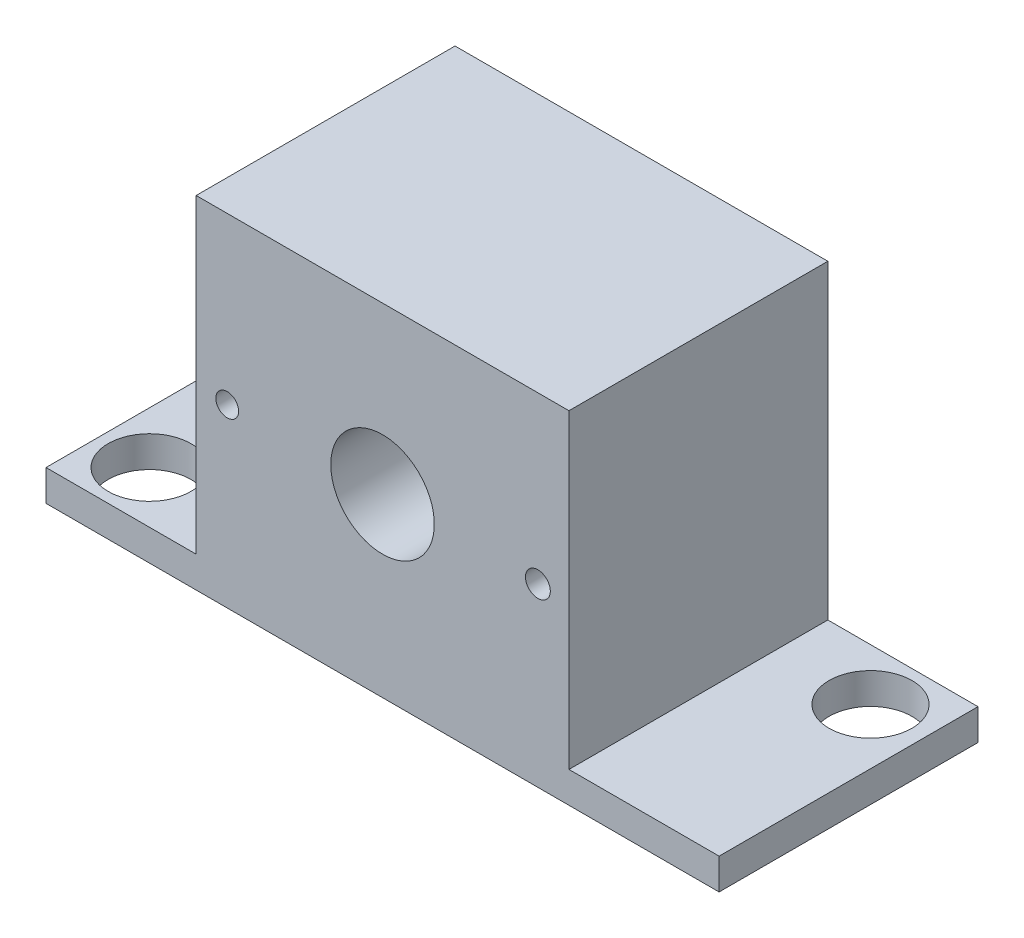
SolidWorks part; units mm, degrees
ref_plane "Front Plane" through (0, 0, 0) normal (0, 0, 1) x (1, 0, 0)
ref_plane "Top Plane" through (0, 0, 0) normal (0, 1, 0) x (1, 0, 0)
ref_plane "Right Plane" through (0, 0, 0) normal (1, 0, 0) x (0, 0, -1)
sketch "Sketch1" plane through (0, 0, 0) normal (0, 1, 0) x (1, 0, 0)
  line L1 (-32.5, 12.5) -> (32.5, 12.5)
  line L2 (-32.5, 12.5) -> (-32.5, -12.5)
  line L3 (-32.5, -12.5) -> (32.5, -12.5)
  line L4 (32.5, 12.5) -> (32.5, -12.5)
  line L5 (-32.5, 12.5) -> (32.5, -12.5) construction
  line L6 (-32.5, -12.5) -> (32.5, 12.5) construction
  circle A0 centre (-27.5, -7.5) radius 4
  circle A1 centre (27.1197, 7.5) radius 4
  point P0 (0, 0)
  dimension "D5" = 8
  dimension "D6" = 8
  dimension "D1" = 25
  dimension "D2" = 65
  dimension "D3" = 56.642
  dimension "D4" = 5
  dimension "D7" = 5
  dimension "D8" = 5
extrude "Boss-Extrude1" add sketch "Sketch1" along normal blind 3
sketch "Sketch2" plane through (0, 0, -12.5) normal (0, 0, -1) x (-1, 0, 0)
  line L0 (-32.5, 3) -> (32.5, 3) construction
  line L1 (-18, 33) -> (18, 33)
  line L2 (-18, 33) -> (-18, 3)
  line L3 (-18, 3) -> (18, 3)
  line L4 (18, 33) -> (18, 3)
  line L5 (-18, 33) -> (18, 3) construction
  line L6 (-18, 3) -> (18, 33) construction
  point P0 (0, 18)
  dimension "D1" = 36
  dimension "D2" = 30
  dimension "D3" = 0
extrude "Boss-Extrude2" add sketch "Sketch2" against normal up to surface (25 mm away) up to face at (0, 1.5, 12.5)
sketch "Sketch3" plane through (0, 0, -12.5) normal (0, 0, -1) x (-1, 0, 0)
  line L0 (-32.5, 3) -> (-18, 3) construction
  line L1 (-15, 30) -> (15, 30)
  line L2 (-15, 30) -> (-15, 19.5)
  line L3 (-15, 4) -> (15, 4)
  line L4 (15, 30) -> (15, 19.5)
  line L5 (-15, 30) -> (15, 4) construction
  line L6 (-15, 4) -> (15, 30) construction
  line L7 (-15, 14.5) -> (-15, 4)
  line L8 (15, 14.5) -> (15, 4)
  arc A0 (-15, 14.5) -> (-15, 19.5) centre (-15, 17) ccw
  arc A1 (15, 19.5) -> (15, 14.5) centre (15, 17) ccw
  point P0 (0, 17)
  dimension "D6" = 2.5
  dimension "D7" = 2.5
  dimension "D1" = 26
  dimension "D2" = 1
  dimension "D3" = 0
  dimension "D4" = 0
  dimension "D5" = 30
  dimension "D8" = 0
extrude "Cut-Extrude1" cut sketch "Sketch3" against normal blind 5 contours L2 A0 L7 L3 L8 A1 L4 L1
sketch "Sketch4" plane through (0, 0, -7.5) normal (0, 0, -1) x (-1, 0, 0)
  circle A0 centre (0, 17) radius 5
  arc A1 (-15, 14.5) -> (-15, 19.5) centre (-15, 17) ccw construction
  dimension "D1" = 10
  dimension "D2" = 0
extrude "Cut-Extrude2" cut sketch "Sketch4" against normal through all
sketch "Sketch5" plane through (0, 0, 12.5) normal (0, 0, 1) x (1, 0, 0)
  circle A0 centre (15, 17) radius 5
  circle A1 centre (-15, 49) radius 5
  dimension "D1" = 10
  dimension "D2" = 10
extrude "Cut-Extrude3" [suppressed] cut sketch "Sketch5" against normal blind 19
sketch "Sketch6" plane through (0, 0, -12.5) normal (0, 0, -1) x (-1, 0, 0)
  circle A0 centre (-15, 17) radius 1.2
  circle A1 centre (15, 17) radius 1.1
  dimension "D1" = 2.4
  dimension "D2" = 2.2
extrude "Cut-Extrude4" cut sketch "Sketch6" against normal through all
